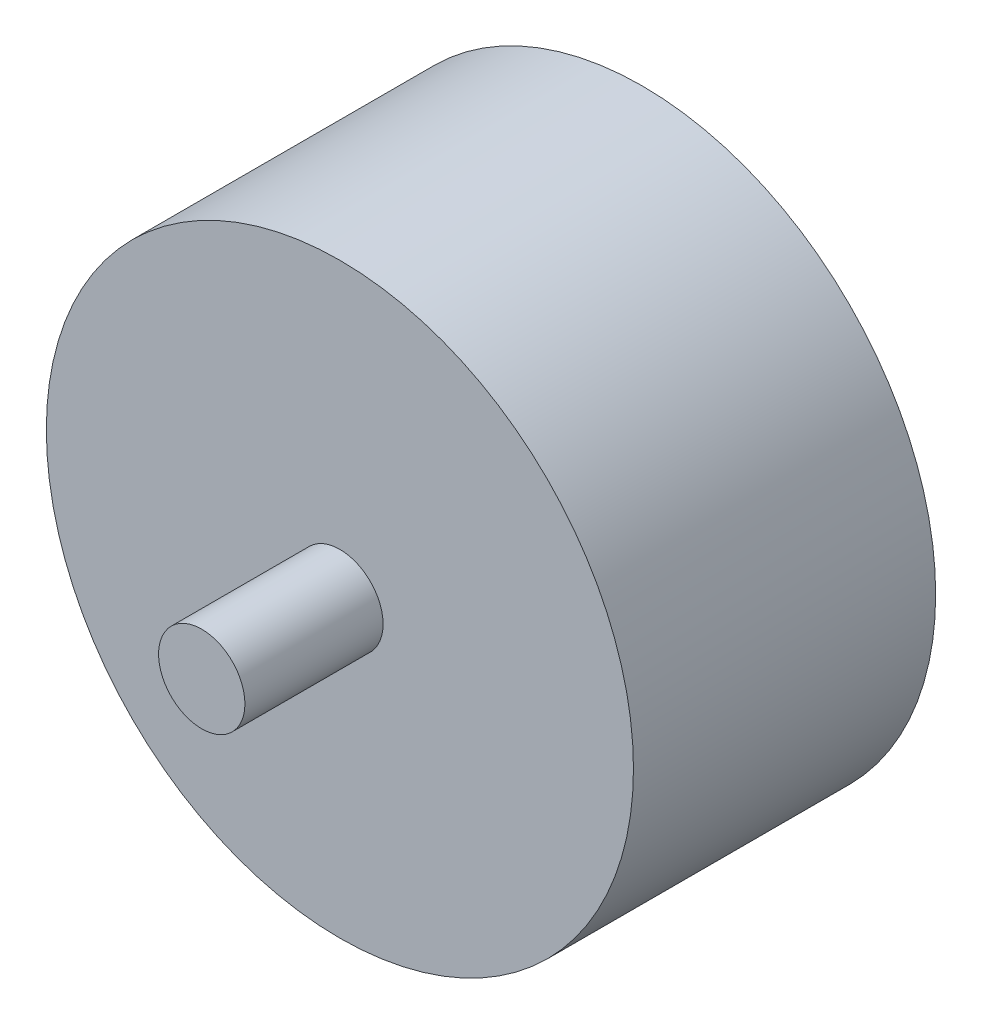
SolidWorks part; units mm, degrees
ref_plane "Front Plane" through (0, 0, 0) normal (0, 0, 1) x (1, 0, 0)
ref_plane "Top Plane" through (0, 0, 0) normal (0, 1, 0) x (1, 0, 0)
ref_plane "Right Plane" through (0, 0, 0) normal (1, 0, 0) x (0, 0, -1)
sketch "Sketch1" plane through (0, 0, 0) normal (0, 0, 1) x (1, 0, 0)
  circle A0 centre (0, 0) radius 17
  dimension "D1" = 34
extrude "Boss-Extrude1" add sketch "Sketch1" along normal blind 25.5
sketch "Sketch2" plane through (0, 0, 25.5) normal (0, 0, 1) x (1, 0, 0)
  circle A0 centre (0, 0) radius 2.5
  circle A1 centre (0, 0) radius 17
  circle A2 centre (0, 0) radius 17 construction
  dimension "D1" = 5
extrude "Cut-Extrude1" cut sketch "Sketch2" against normal blind 8
